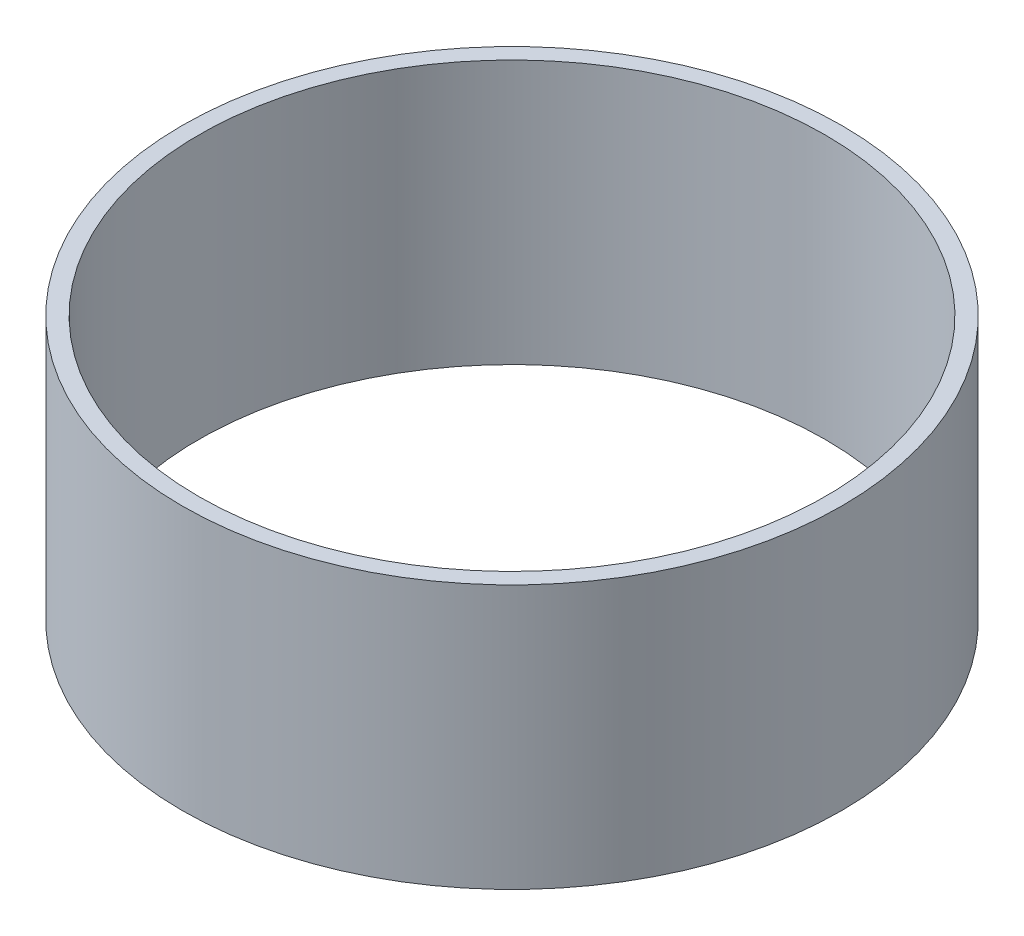
SolidWorks part; units mm, degrees
ref_plane "前视基准面" through (0, 0, 0) normal (0, 0, 1) x (1, 0, 0)
ref_plane "上视基准面" through (0, 0, 0) normal (0, 1, 0) x (1, 0, 0)
ref_plane "右视基准面" through (0, 0, 0) normal (1, 0, 0) x (0, 0, -1)
sketch "草图1" plane through (0, 0, 0) normal (0, 1, 0) x (1, 0, 0)
  circle A0 centre (0, 0) radius 700
  dimension "D1" = 1400
extrude "凸台-拉伸1" add sketch "草图1" along normal blind 560
sketch "草图2" plane through (0, 560, 0) normal (0, 1, 0) x (1, 0, 0)
  circle A0 centre (0, 0) radius 665
  dimension "D1" = 1330
extrude "切除-拉伸1" cut sketch "草图2" against normal blind 560
